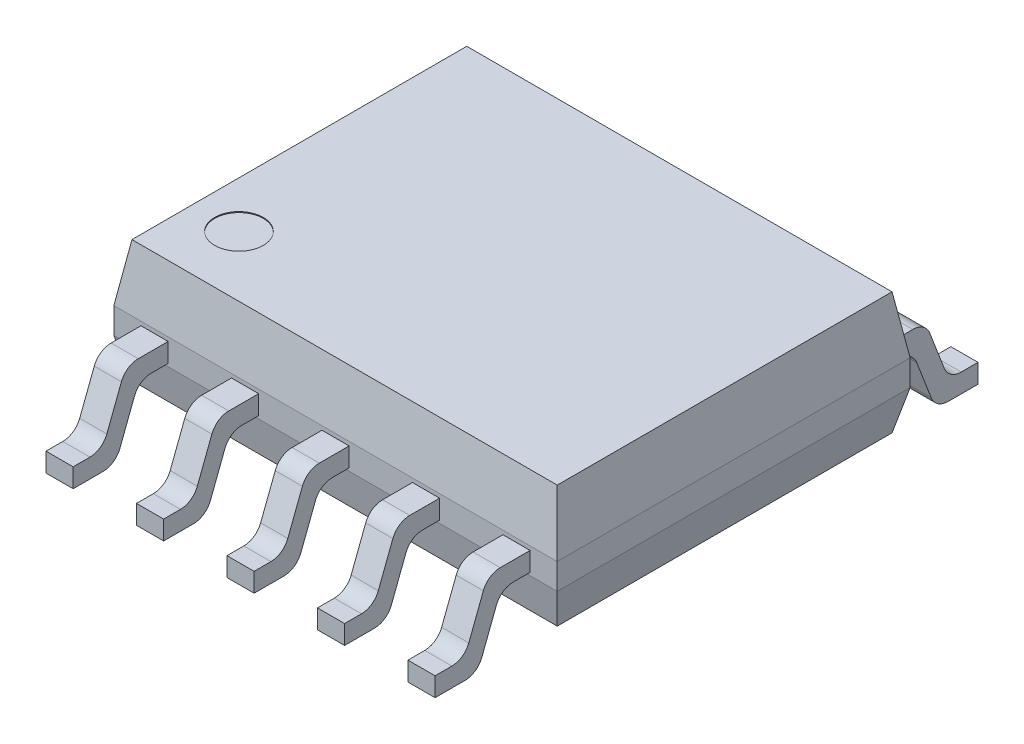
SolidWorks part; units mm, degrees
ref_plane "Front" through (0, 0, 0) normal (0, 0, 1) x (1, 0, 0)
ref_plane "Top" through (0, 0, 0) normal (0, 1, 0) x (1, 0, 0)
ref_plane "Right" through (0, 0, 0) normal (1, 0, 0) x (0, 0, -1)
sketch "Sketch1" plane through (0, 0, 0) normal (0, 1, 0) x (1, 0, 0)
  line L1 (2.45, 1.95) -> (-2.45, 1.95)
  line L2 (2.45, 1.95) -> (2.45, -1.95)
  line L3 (2.45, -1.95) -> (-2.45, -1.95)
  line L4 (-2.45, 1.95) -> (-2.45, -1.95)
  line L5 (2.45, 1.95) -> (-2.45, -1.95) construction
  line L6 (2.45, -1.95) -> (-2.45, 1.95) construction
  point P0 (0, 0)
  dimension "D1" = 4.9
  dimension "D2" = 3.9
extrude "Boss-Extrude1" add sketch "Sketch1" along normal blind 1.35
sketch "Sketch2" plane through (2.45, 0, 0) normal (1, 0, 0) x (0, 0, -1)
  line L0 (-1.95, 0.465) -> (-2.2731, 0.465)
  line L1 (-1.95, 1.35) -> (-1.95, 0) construction
  line L2 (-2.2731, 0.465) -> (-2.5326, -0.21)
  line L3 (-2.5326, -0.21) -> (-3, -0.21)
  line L4 (-1.95, 0.675) -> (-2.4174, 0.675)
  line L5 (-2.4174, 0.675) -> (-2.6769, 0)
  line L6 (-2.6769, 0) -> (-3, 0)
  line L7 (-3, 0) -> (-3, -0.21)
  line L8 (-1.95, 0.675) -> (-1.95, 0.465)
  line L9 (-2.5471, 0.3375) -> (-2.3511, 0.2621) construction
  line L10 (-1.95, 0) -> (1.95, 0) construction
  dimension "D1" = 0.21
  dimension "D2" = 3
  dimension "D3" = 111.028
extrude "Boss-Extrude2" add sketch "Sketch2" against normal up to vertex (4.9 mm away) separate body up to point (-2.45, 1.35, 1.95)
fillet "Fillet1" radius 0.2 4 edges at (0, -0.21, 2.5326) (0, 0.465, 2.2731) (0, 0, 2.6769) (0, 0.675, 2.4174)
sketch "Sketch3" plane through (0, 1.35, 0) normal (0, 1, 0) x (1, 0, 0)
  line L0 (-2.45, -1.95) -> (2.45, -1.95) construction
  line L1 (-0.15, -1.95) -> (0.15, -1.95)
  line L2 (-0.15, -1.95) -> (-0.15, -3)
  line L3 (-0.15, -3) -> (0.15, -3)
  line L4 (0.15, -1.95) -> (0.15, -3)
  line L5 (0, -3) -> (0, -1.95) construction
  line L6 (-0.15, -2.475) -> (0.15, -2.475) construction
  line L7 (-2.45, -3) -> (2.45, -3) construction
  line L8 (0.85, -1.95) -> (1.15, -1.95)
  line L9 (0.85, -1.95) -> (0.85, -3)
  line L10 (0.85, -3) -> (1.15, -3)
  line L11 (1.15, -1.95) -> (1.15, -3)
  line L12 (1, -3) -> (1, -1.95) construction
  line L13 (0.85, -2.475) -> (1.15, -2.475) construction
  line L14 (1.85, -1.95) -> (2.15, -1.95)
  line L15 (1.85, -1.95) -> (1.85, -3)
  line L16 (1.85, -3) -> (2.15, -3)
  line L17 (2.15, -1.95) -> (2.15, -3)
  line L18 (2, -3) -> (2, -1.95) construction
  line L19 (1.85, -2.475) -> (2.15, -2.475) construction
  line L20 (-0.15, -1.95) -> (0.15, -1.95)
  line L21 (-0.15, -1.95) -> (-0.15, -3)
  line L22 (-0.15, -3) -> (0.15, -3)
  line L23 (0.15, -1.95) -> (0.15, -3)
  line L24 (0, -3) -> (0, -1.95) construction
  line L25 (-0.15, -2.475) -> (0.15, -2.475) construction
  line L26 (0.85, -1.95) -> (1.15, -1.95)
  line L27 (0.85, -1.95) -> (0.85, -3)
  line L28 (0.85, -3) -> (1.15, -3)
  line L29 (1.15, -1.95) -> (1.15, -3)
  line L30 (1, -3) -> (1, -1.95) construction
  line L31 (0.85, -2.475) -> (1.15, -2.475) construction
  line L32 (-1.15, -1.95) -> (-0.85, -1.95)
  line L33 (-1.15, -1.95) -> (-1.15, -3)
  line L34 (-1.15, -3) -> (-0.85, -3)
  line L35 (-0.85, -1.95) -> (-0.85, -3)
  line L36 (-1, -3) -> (-1, -1.95) construction
  line L37 (-1.15, -2.475) -> (-0.85, -2.475) construction
  line L38 (-0.15, -1.95) -> (0.15, -1.95)
  line L39 (-0.15, -1.95) -> (-0.15, -3)
  line L40 (-0.15, -3) -> (0.15, -3)
  line L41 (0.15, -1.95) -> (0.15, -3)
  line L42 (0, -3) -> (0, -1.95) construction
  line L43 (-0.15, -2.475) -> (0.15, -2.475) construction
  line L44 (-1.15, -1.95) -> (-0.85, -1.95)
  line L45 (-1.15, -1.95) -> (-1.15, -3)
  line L46 (-1.15, -3) -> (-0.85, -3)
  line L47 (-0.85, -1.95) -> (-0.85, -3)
  line L48 (-1, -3) -> (-1, -1.95) construction
  line L49 (-1.15, -2.475) -> (-0.85, -2.475) construction
  line L50 (-2.15, -1.95) -> (-1.85, -1.95)
  line L51 (-2.15, -1.95) -> (-2.15, -3)
  line L52 (-2.15, -3) -> (-1.85, -3)
  line L53 (-1.85, -1.95) -> (-1.85, -3)
  line L54 (-2, -3) -> (-2, -1.95) construction
  line L55 (-2.15, -2.475) -> (-1.85, -2.475) construction
  line L56 (0, -2.475) -> (1, -2.475) construction
  line L57 (0, -2.475) -> (-1, -2.475) construction
  point P18 (1, -2.475)
  point P27 (2, -2.475)
  point P36 (0, -2.475)
  point P45 (1, -2.475)
  point P54 (-1, -2.475)
  point P63 (0, -2.475)
  point P72 (-1, -2.475)
  point P81 (-2, -2.475)
  point P96 (0, -2.475)
  dimension "D1" = 0.3
  dimension "D4" = 1
  dimension "D5" = 1
  dimension "D2" = 3
  dimension "D3" = 3
extrude "Cut-Extrude1" cut sketch "Sketch3" against normal through all flip side to cut contours L53 L52 L51 L50 | L33 L34 L35 L32 | L2 L3 L4 L1 | L9 L10 L11 L8 | L15 L16 L17 L14
mirror "Mirror2" about plane through (0, 0, 0) normal (0, 0, 1) of bodies 106 107 105 104 103
chamfer "Chamfer1" distance 0.1 angle 77 4 edges at (2.45, 0, 0) (0, 0, -1.95) (-2.45, 0, 0) (0, 0, 1.95)
chamfer "Chamfer2" distance 0.1 angle 81 4 edges at (-2.45, 1.35, 0) (0, 1.35, 1.95) (2.45, 1.35, 0) (0, 1.35, -1.95)
sketch "Sketch4" plane through (0, 1.35, 0) normal (0, 1, 0) x (1, 0, 0)
  circle A0 centre (-1.8368, -1.1806) radius 0.2686
  dimension "D1" = 0.5372
  dimension "D2" = 1.8368
  dimension "D3" = 1.1806
extrude "Cut-Extrude2" cut sketch "Sketch4" against normal blind 0.01
